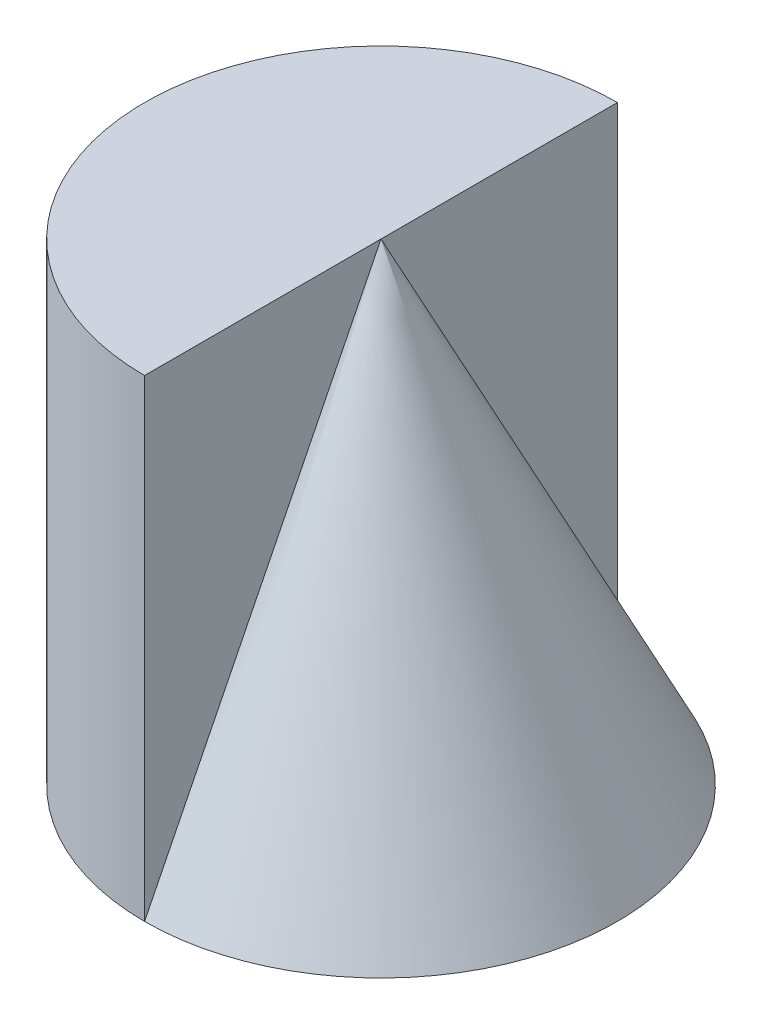
SolidWorks part; units mm, degrees
ref_plane "Front" through (0, 0, 0) normal (0, 0, 1) x (1, 0, 0)
ref_plane "Top" through (0, 0, 0) normal (0, 1, 0) x (1, 0, 0)
ref_plane "Right" through (0, 0, 0) normal (1, 0, 0) x (0, 0, -1)
sketch "Sketch1" plane through (0, 0, 0) normal (0, 0, 1) x (1, 0, 0)
  line L1 (0, 0) -> (2, 0)
  line L2 (0, 0) -> (0, 4)
  line L3 (0, 4) -> (2, 4)
  line L4 (2, 0) -> (2, 4)
  dimension "D1" = 2
  dimension "D2" = 4
extrude "Boss-Extrude1" add sketch "Sketch1" along normal blind 4
sketch "Sketch2" plane through (2, 0, 0) normal (1, 0, 0) x (0, 0, -1)
  line L0 (-2, 0) -> (-2, 2.3525) construction
  line L1 (-4, 0) -> (0, 0) construction
  line L2 (-2, 0) -> (-2, 4)
  line L3 (-4, 4) -> (0, 4) construction
  line L4 (-2, 4) -> (0, 0)
  line L5 (0, 0) -> (-2, 0)
revolve "Revolve1" add sketch "Sketch2" angle 180 about L2
sketch "Sketch3" plane through (0, 4, 0) normal (0, 1, 0) x (1, 0, 0)
  line L0 (2, 0) -> (2, -4)
  arc A0 (2, 0) -> (2, -4) centre (2, -2) ccw
  line M3 (2, 0) -> (0, 0)
  line M4 (0, 0) -> (0, -4)
  line M5 (0, -4) -> (2, -4)
  dimension "D1" = 2
extrude "Cut-Extrude1" cut sketch "Sketch3" against normal blind 4 contours A0 M4 M5 | A0 M3 M4
